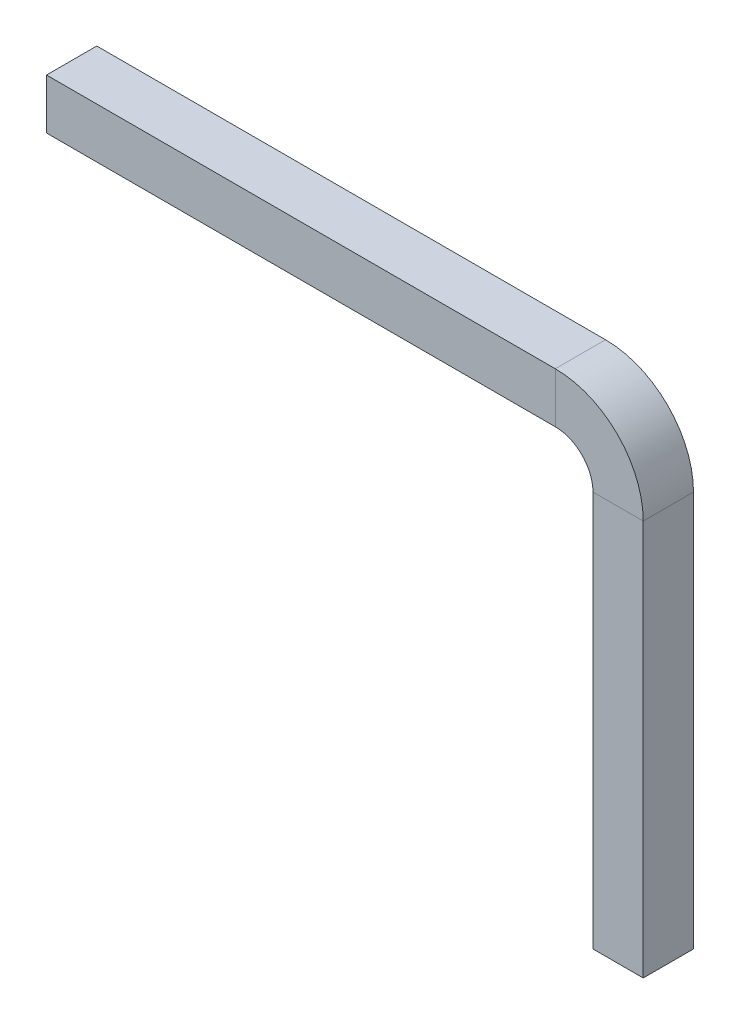
SolidWorks part; units mm, degrees
ref_plane "Front Plane" through (0, 0, 0) normal (0, 0, 1) x (1, 0, 0)
ref_plane "Top Plane" through (0, 0, 0) normal (0, 1, 0) x (1, 0, 0)
ref_plane "Right Plane" through (0, 0, 0) normal (1, 0, 0) x (0, 0, -1)
sketch "Sketch1" plane through (0, 0, 0) normal (0, 0, 1) x (1, 0, 0)
  line L0 (-9.3, 0) -> (-1, 0)
  line L1 (0, -1) -> (0, -7.5)
  arc A0 (0, -1) -> (-1, 0) centre (-1, -1) ccw
  point P6 (0, 0)
  dimension "D3" = 1
  dimension "D1" = 9.3
  dimension "D2" = 7.5
ref_plane "Plane1" through (-9.3, 0, 0) normal (1, 0, 0) x (0, 0, -1)
sketch "Sketch2" plane through (-9.3, 0, 0) normal (1, 0, 0) x (0, 0, -1)
  line L1 (0.4, 0.4) -> (-0.4, 0.4)
  line L2 (0.4, 0.4) -> (0.4, -0.4)
  line L3 (0.4, -0.4) -> (-0.4, -0.4)
  line L4 (-0.4, 0.4) -> (-0.4, -0.4)
  line L5 (0.4, 0.4) -> (-0.4, -0.4) construction
  line L6 (0.4, -0.4) -> (-0.4, 0.4) construction
  point P0 (0, 0)
  dimension "D1" = 0.8
  dimension "D2" = 0.8
sweep "Sweep1" add profiles "Sketch2" path "Sketch1"
chamfer "Chamfer1" distance 0.2 angle 45 8 edges at (0.4, -7.5, 0) (0, -7.5, -0.4) (-0.4, -7.5, 0) (0, -7.5, 0.4) (-9.3, -0.4, 0) (-9.3, 0, -0.4) (-9.3, 0.4, 0) (-9.3, 0, 0.4)
